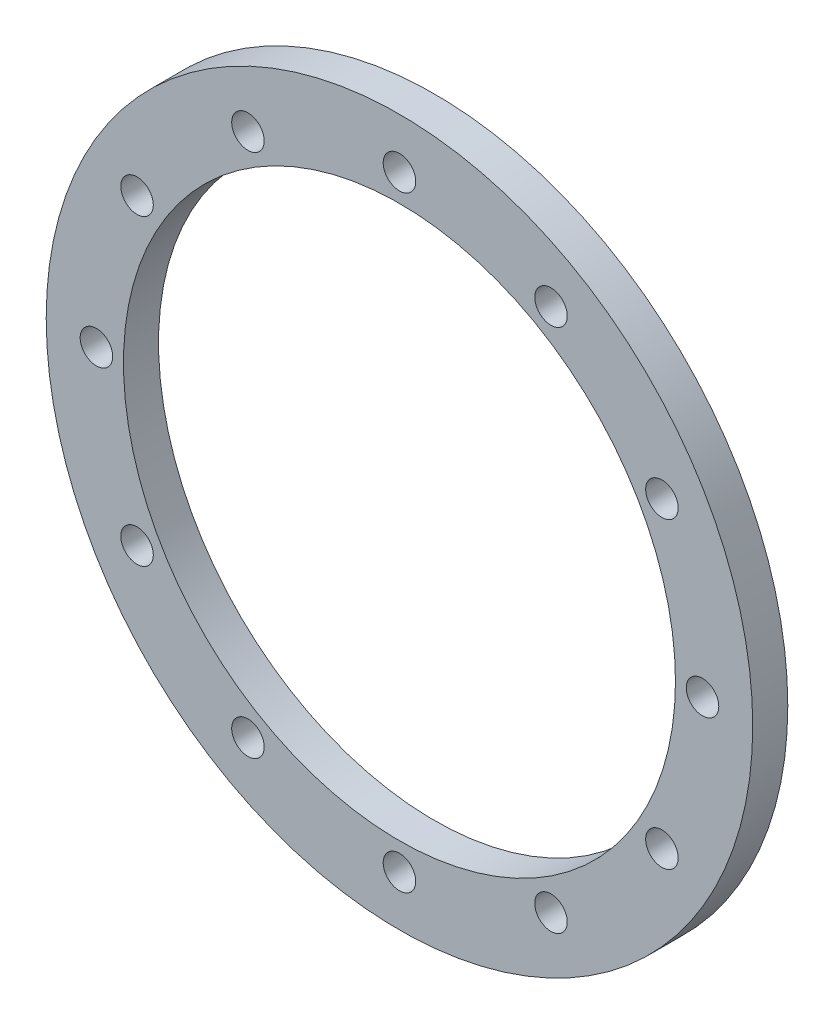
SolidWorks part; units mm, degrees
ref_plane "Front Plane" through (0, 0, 0) normal (0, 0, 1) x (1, 0, 0)
ref_plane "Top Plane" through (0, 0, 0) normal (0, 1, 0) x (1, 0, 0)
ref_plane "Right Plane" through (0, 0, 0) normal (1, 0, 0) x (0, 0, -1)
sketch "Sketch1" plane through (0, 0, 0.2) normal (0, 0, 1) x (1, 0, 0)
  circle A0 centre (-17.5, -28.25) radius 25 construction
  circle A1 centre (-17.5, -28.25) radius 25
  circle A2 centre (-17.5, -28.25) radius 32
  circle A3 centre (-17.5, -55.7) radius 1.1303 construction
  circle A4 centre (-17.5, -55.7) radius 1.1303 construction
  circle A5 centre (-17.5, -55.7) radius 1.4732
  circle A6 centre (-31.225, -52.0224) radius 1.4732
  circle A7 centre (-41.2724, -41.975) radius 1.4732
  circle A8 centre (-44.95, -28.25) radius 1.4732
  circle A9 centre (-41.2724, -14.525) radius 1.4732
  circle A10 centre (-31.225, -4.4776) radius 1.4732
  circle A11 centre (-17.5, -0.8) radius 1.4732
  circle A12 centre (-3.775, -4.4776) radius 1.4732
  circle A13 centre (6.2724, -14.525) radius 1.4732
  circle A14 centre (9.95, -28.25) radius 1.4732
  circle A15 centre (6.2724, -41.975) radius 1.4732
  circle A16 centre (-3.775, -52.0224) radius 1.4732
  point P33 (-17.5, -28.25)
  dimension "D1" = 64
  dimension "D2" = 2.9464
  dimension "D3" = 12
extrude "Boss-Extrude1" add sketch "Sketch1" along normal blind 3.175
